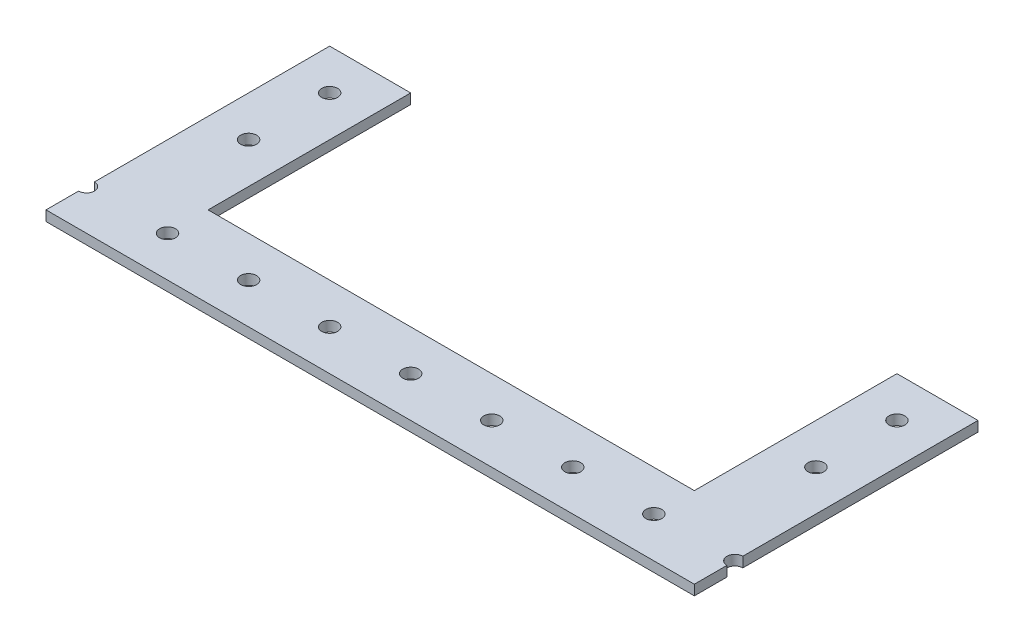
SolidWorks part; units mm, degrees
ref_plane "Front" through (0, 0, 0) normal (0, 0, 1) x (1, 0, 0)
ref_plane "Top" through (0, 0, 0) normal (0, 1, 0) x (1, 0, 0)
ref_plane "Right" through (0, 0, 0) normal (1, 0, 0) x (0, 0, -1)
sketch "Sketch1" plane through (0, 0, 0) normal (0, 1, 0) x (1, 0, 0)
  line L0 (-101.6, 0) -> (101.6, 0)
  line L1 (101.6, 0) -> (101.6, 88.9)
  line L2 (101.6, 88.9) -> (76.2, 88.9)
  line L3 (76.2, 88.9) -> (76.2, 25.4)
  line L4 (76.2, 25.4) -> (-76.2, 25.4)
  line L5 (-76.2, 25.4) -> (-76.2, 88.9)
  line L6 (-76.2, 88.9) -> (-101.6, 88.9)
  line L7 (-101.6, 88.9) -> (-101.6, 0)
  line L8 (-76.2, 25.4) -> (-76.2, 0) construction
  line L9 (-101.6, 12.7) -> (101.6, 12.7) construction
  circle A0 centre (-101.6, 12.7) radius 2.4892
  circle A1 centre (-76.2, 12.7) radius 2.4892
  circle A2 centre (-50.8, 12.7) radius 2.4892
  circle A3 centre (-25.4, 12.7) radius 2.4892
  circle A4 centre (0, 12.7) radius 2.4892
  circle A5 centre (25.4, 12.7) radius 2.4892
  circle A6 centre (50.8, 12.7) radius 2.4892
  circle A7 centre (76.2, 12.7) radius 2.4892
  circle A8 centre (101.6, 12.7) radius 2.4892
  point P4 (0, 0)
  point P14 (-76.2, 12.7)
  dimension "D6" = 4.9784
  dimension "D1" = 25.4
  dimension "D2" = 25.4
  dimension "D3" = 152.4
  dimension "D4" = 63.5
  dimension "D7" = 9
extrude "Boss-Extrude1" add sketch "Sketch1" along normal blind 3.175 contours A8 L1 L2 L3 L4 L5 L6 L7 A0 L0 A7 A6 A5 A4 A3 A2 A1
sketch "Sketch2" plane through (0, 3.175, 0) normal (0, 1, 0) x (1, 0, 0)
  line L0 (-101.6, 76.2) -> (101.6, 76.2) construction
  line L3 (101.6, 50.8) -> (-101.6, 50.8) construction
  line L4 (88.9, 88.9) -> (88.9, 0) construction
  line L7 (-88.9, 88.9) -> (-88.9, 0) construction
  line L9 (-101.6, 0) -> (101.6, 0) construction
  line L10 (-101.6, 88.9) -> (-101.6, 15.1892) construction
  line L11 (101.6, 88.9) -> (76.2, 88.9) construction
  line L12 (101.6, 15.1892) -> (101.6, 88.9) construction
  line L13 (-76.2, 88.9) -> (-101.6, 88.9) construction
  circle A0 centre (-88.9, 50.8) radius 2.4892
  circle A1 centre (-88.9, 76.2) radius 2.4892
  circle A2 centre (88.9, 76.2) radius 2.4892
  circle A3 centre (88.9, 50.8) radius 2.4892
  dimension "D1" = 4.9784
  dimension "D2" = 12.7
  dimension "D3" = 25.4
extrude "Cut-Extrude1" cut sketch "Sketch2" against normal through all
